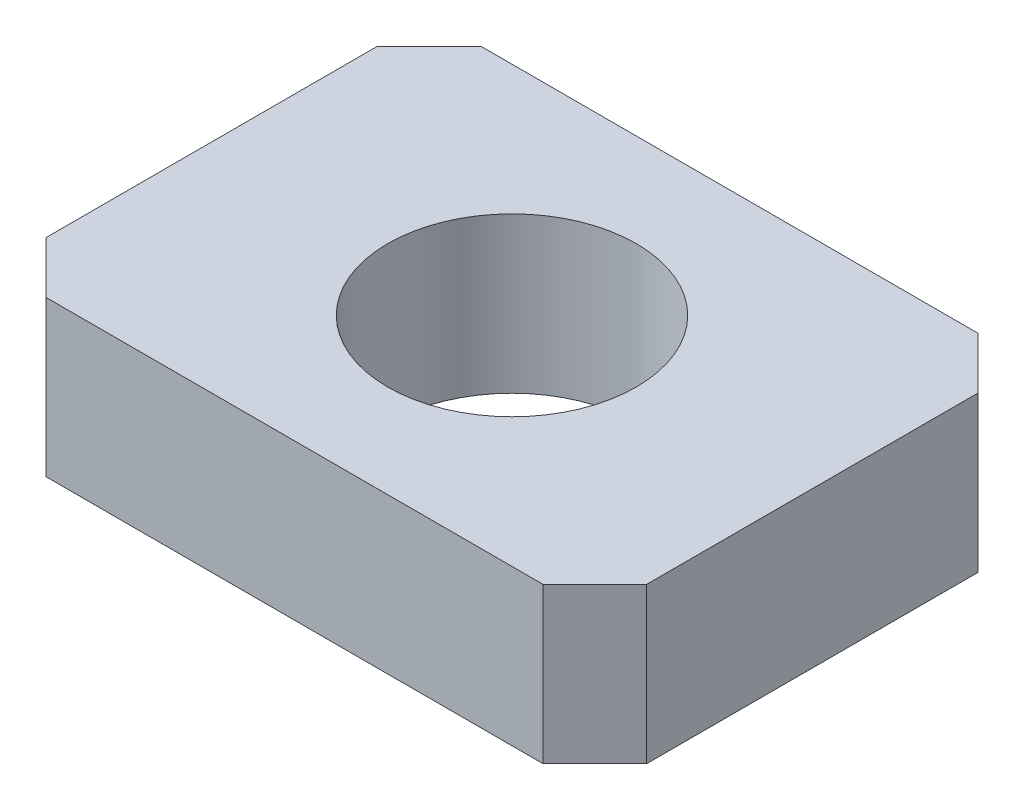
SolidWorks part; units mm, degrees
ref_plane "Front Plane" through (0, 0, 0) normal (0, 0, 1) x (1, 0, 0)
ref_plane "Top Plane" through (0, 0, 0) normal (0, 1, 0) x (1, 0, 0)
ref_plane "Right Plane" through (0, 0, 0) normal (1, 0, 0) x (0, 0, -1)
sketch "Sketch1" plane through (0, 0, 0) normal (0, 1, 0) x (1, 0, 0)
  line L1 (-2.9, -2.1) -> (2.9, -2.1)
  line L3 (-2.9, 2.1) -> (2.9, 2.1)
  line L5 (-2.9, -2.1) -> (2.9, 2.1) construction
  line L6 (-2.9, 2.1) -> (2.9, -2.1) construction
  line L9 (0, 0) -> (0, -2.1) construction
  line L15 (-2.9, 2.1) -> (-2.9, -2.1)
  line L16 (2.9, -2.1) -> (2.9, 2.1)
  circle A0 centre (0, 0) radius 1.2
  point P0 (0, 0)
  dimension "D4" = 2.4
  dimension "D1" = 4.2
  dimension "D2" = 4.2
  dimension "D3" = 5.8
extrude "Boss-Extrude1" add sketch "Sketch1" along normal blind 1.5
chamfer "Chamfer1" distance 0.5 angle 45 4 edges at (2.9, 0.75, -2.1) (2.9, 0.75, 2.1) (-2.9, 0.75, 2.1) (-2.9, 0.75, -2.1)
